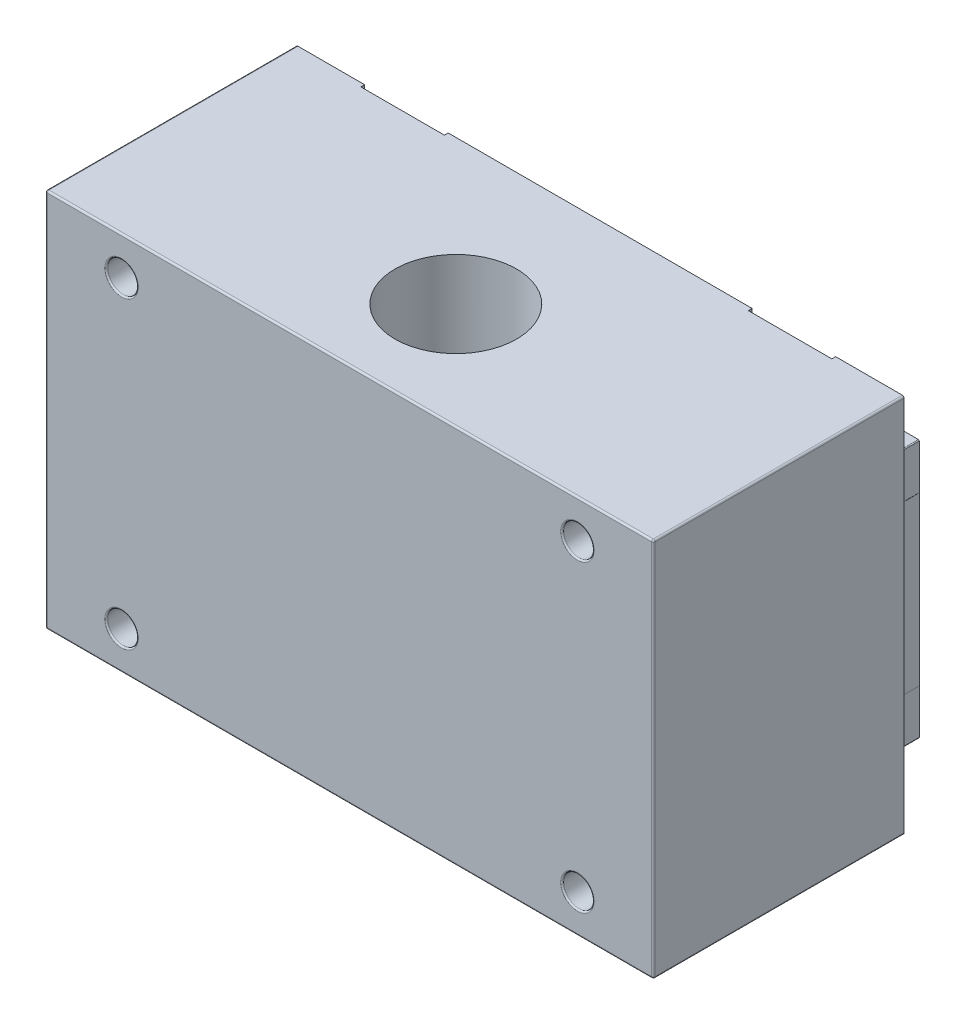
SolidWorks part; units mm, degrees
ref_plane "前视基准面" through (0, 0, 0) normal (0, 0, 1) x (1, 0, 0)
ref_plane "上视基准面" through (0, 0, 0) normal (0, 1, 0) x (1, 0, 0)
ref_plane "右视基准面" through (0, 0, 0) normal (1, 0, 0) x (0, 0, -1)
sketch "草图1" plane through (0, 0, 0) normal (0, 1, 0) x (1, 0, 0)
  line L0 (0, 0) -> (7, 0)
  line L9 (7, 0) -> (7, -4.5)
  line L18 (7, -4.5) -> (18, -4.5)
  line L19 (18, -4.5) -> (18, 0)
  line L20 (18, 0) -> (25, 0)
  line L21 (25, 0) -> (25, -9)
  line L22 (25, -9) -> (0, -9)
  line L23 (0, -9) -> (0, 0)
  line L33 (51, 0) -> (51, -9)
  line L34 (51, -9) -> (76, -9)
  line L35 (51, 0) -> (58, 0)
  line L36 (58, 0) -> (58, -4.5)
  line L37 (58, -4.5) -> (69, -4.5)
  line L38 (69, -4.5) -> (69, 0)
  line L39 (69, 0) -> (76, 0)
  line L40 (76, 0) -> (76, -9)
extrude "凸台-拉伸1" add sketch "草图1" along normal blind 6
sketch "草图2" plane through (0, 6, 0) normal (0, 1, 0) x (1, 0, 0)
  line L0 (7, 0) -> (-0.02, 0)
  line L1 (-0.02, 0) -> (-0.02, -10)
  line L2 (-0.02, -10) -> (25.02, -10)
  line L3 (25.02, -10) -> (25.02, 0)
  line L4 (25.02, 0) -> (18, 0)
  line L5 (18, 0) -> (18, -4.5)
  line L6 (18, -4.5) -> (7, -4.5)
  line L7 (7, -4.5) -> (7, 0)
  line L8 (58, 0) -> (50.98, 0)
  line L9 (50.98, 0) -> (50.98, -10)
  line L10 (50.98, -10) -> (76.02, -10)
  line L11 (76.02, -10) -> (76.02, 0)
  line L12 (76.02, 0) -> (69, 0)
  line L13 (69, 0) -> (69, -4.5)
  line L14 (69, -4.5) -> (58, -4.5)
  line L15 (58, -4.5) -> (58, 0)
extrude "凸台-拉伸2" add sketch "草图2" along normal blind 22
sketch "草图3" plane through (0, 28, 0) normal (0, 1, 0) x (1, 0, 0)
  line L0 (7, 0) -> (0, 0)
  line L1 (0, 0) -> (0, -9)
  line L2 (0, -9) -> (25, -9)
  line L3 (25, -9) -> (25, 0)
  line L4 (25, 0) -> (18, 0)
  line L5 (18, 0) -> (18, -4.5)
  line L6 (18, -4.5) -> (7, -4.5)
  line L7 (7, -4.5) -> (7, 0)
  line L8 (58, 0) -> (51, 0)
  line L9 (51, 0) -> (51, -9)
  line L10 (51, -9) -> (76, -9)
  line L11 (76, -9) -> (76, 0)
  line L12 (76, 0) -> (69, 0)
  line L13 (69, 0) -> (69, -4.5)
  line L14 (69, -4.5) -> (58, -4.5)
  line L15 (58, -4.5) -> (58, 0)
extrude "凸台-拉伸3" add sketch "草图3" along normal blind 6
fillet "圆角1" radius 0.2 4 edges at (25, 3, 9) (0, 3, 9) (25, 31, 9) (0, 31, 9)
fillet "圆角2" radius 0.12 10 edges at (0, 0, 4.4) (0.0586, 0, 8.9414) (12.5, 0, 9) (24.9414, 0, 8.9414) (25, 0, 4.4) (25, 34, 4.4) (24.9414, 34, 8.9414) (12.5, 34, 9) (0.0586, 34, 8.9414) (0, 34, 4.4)
fillet "圆角3" radius 0.36 2 edges at (25.02, 17, 10) (-0.02, 17, 10)
fillet "圆角4" radius 0.2 4 edges at (76, 3, 9) (51, 3, 9) (51, 31, 9) (76, 31, 9)
fillet "圆角5" radius 0.12 10 edges at (51, 0, 4.4) (51.0586, 0, 8.9414) (63.5, 0, 9) (75.9414, 0, 8.9414) (76, 0, 4.4) (76, 34, 4.4) (75.9414, 34, 8.9414) (63.5, 34, 9) (51.0586, 34, 8.9414) (51, 34, 4.4)
fillet "圆角6" radius 0.36 2 edges at (76.02, 17, 10) (50.98, 17, 10)
ref_plane "基准面4" through (0, -8, 0) normal (0, -1, 0) x (-1, 0, 0)
sketch "草图4" plane through (0, -8, 0) normal (0, -1, 0) x (-1, 0, 0)
  line L0 (-7, -4.5) -> (-7, -4)
  line L1 (-7, -4.5) -> (-7, 0) construction
  line L2 (-7, -4) -> (2, -4)
  line L3 (2, -4) -> (2, -37)
  line L4 (2, -37) -> (-78, -37)
  line L6 (-7, -4.5) -> (-18, -4.5)
  line L7 (-18, -4.5) -> (-18, -4)
  line L8 (-18, 0) -> (-18, -4.5) construction
  line L9 (-18, -4) -> (-58, -4)
  line L10 (-58, -4.5) -> (-58, 0) construction
  line L11 (-58, -4) -> (-58, -4.5)
  line L12 (-58, -4.5) -> (-69, -4.5)
  line L13 (-69, -4.5) -> (-69, -4)
  line L14 (-69, 0) -> (-69, -4.5) construction
  line L15 (-69, -4) -> (-78, -4)
  line L16 (-78, -4) -> (-78, -37)
extrude "凸台-拉伸12" add sketch "草图4" against normal blind 8
sketch "草图5" plane through (0, 34, 0) normal (0, 1, 0) x (1, 0, 0)
  line L0 (7, -4) -> (7, -4.5)
  line L1 (7, -4.5) -> (18, -4.5)
  line L2 (18, -4.5) -> (18, -4)
  line L3 (18, -4) -> (58, -4)
  line L4 (58, -4) -> (58, -4.5)
  line L5 (58, -4.5) -> (69, -4.5)
  line L6 (69, -4.5) -> (69, -4)
  line L7 (69, -4) -> (78, -4)
  line L8 (78, -4) -> (78, -37)
  line L9 (78, -37) -> (-2, -37)
  line L10 (-2, -37) -> (-2, -4)
  line L11 (-2, -4) -> (7, -4)
extrude "凸台-拉伸13" add sketch "草图5" along normal blind 8
sketch "草图6" plane through (0, 0, 0) normal (0, 1, 0) x (1, 0, 0)
  line L1 (0, -8.8) -> (0, 0) construction
  line L2 (0, -4.5) -> (-2, -4.5)
  line L3 (-2, -4) -> (-2, -37) construction
  line L4 (-2, -4.5) -> (-2, -37)
  line L5 (-2, -37) -> (78, -37)
  line L6 (78, -37) -> (78, -4)
  line L7 (78, -4) -> (76, -4)
  line L8 (78, -4) -> (69, -4) construction
  line L9 (76, 0) -> (76, -8.8) construction
  line L10 (76, -4) -> (76, -10.001)
  line L11 (76, -10.001) -> (0, -10.001)
  line L12 (0, -10.001) -> (0, -4.5)
extrude "凸台-拉伸14" add sketch "草图6" along normal blind 34
sketch "草图7" plane through (0, 42, 0) normal (0, 1, 0) x (1, 0, 0)
  circle A0 centre (38, -23) radius 8
extrude "切除-拉伸1" cut sketch "草图7" against normal blind 50
sketch "草图8" plane through (0, -8, 0) normal (0, -1, 0) x (1, 0, 0)
  circle A0 centre (38, 23) radius 10
extrude "切除-拉伸2" cut sketch "草图8" against normal blind 5
sketch "草图9" plane through (0, -3, 0) normal (0, -1, 0) x (1, 0, 0)
  circle A0 centre (38, 23) radius 8.01
  circle A1 centre (38, 23) radius 9.7614
extrude "凸台-拉伸16" add sketch "草图9" along normal blind 4.77
sketch "草图10" plane through (0, 0, 37) normal (0, 0, 1) x (1, 0, 0)
  circle A4 centre (8, 37) radius 2
  circle A5 centre (8, -3) radius 2
  circle A6 centre (68, -3) radius 2
  circle A7 centre (68, 37) radius 2
extrude "切除-拉伸3" cut sketch "草图10" against normal blind 5
fillet "圆角7" radius 0.2 4 edges at (70, 37, 37) (10, -3, 37) (10, 37, 37) (70, -3, 37)
fillet "圆角8" radius 0.23 8 edges at (38, 42, 37) (78, 17, 37) (-2, 17, 37) (38, -8, 37) (-2, -8, 20.5) (78, -8, 20.5) (-2, 42, 20.5) (78, 42, 20.5)
